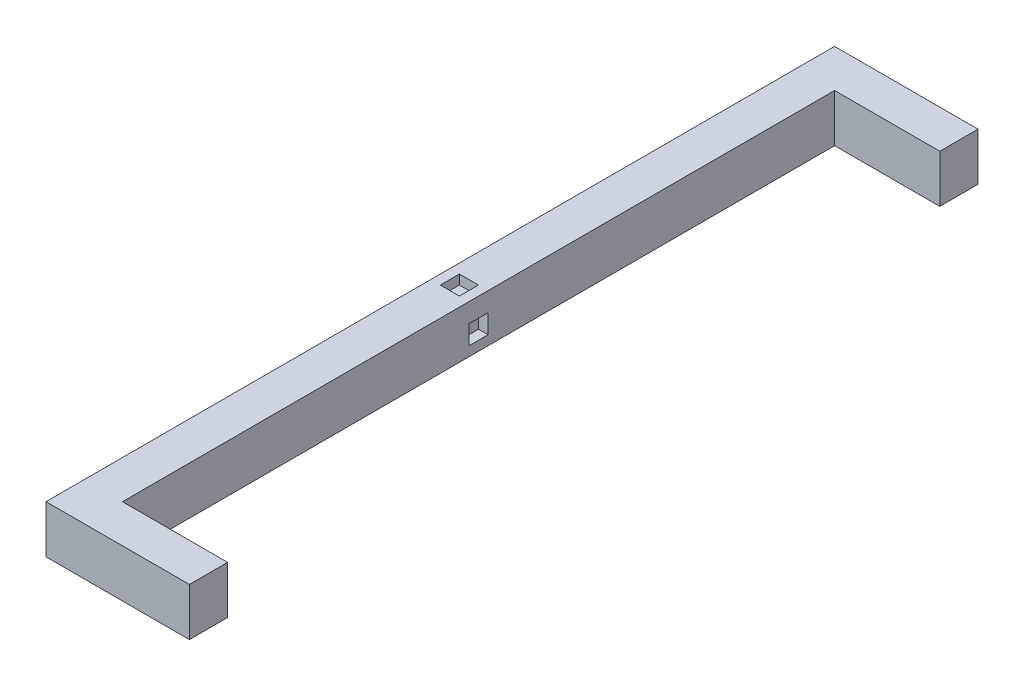
SolidWorks part; units mm, degrees
ref_plane "Front Plane" through (0, 0, 0) normal (0, 0, 1) x (1, 0, 0)
ref_plane "Top Plane" through (0, 0, 0) normal (0, 1, 0) x (1, 0, 0)
ref_plane "Right Plane" through (0, 0, 0) normal (1, 0, 0) x (0, 0, -1)
sketch "Sketch1" plane through (0, 0, 0) normal (0, 0, 1) x (1, 0, 0)
  line L1 (0, 0) -> (8, 0)
  line L2 (0, 0) -> (0, 10)
  line L3 (0, 10) -> (8, 10)
  line L4 (8, 0) -> (8, 10)
  dimension "D1" = 8
  dimension "D2" = 10
extrude "Boss-Extrude1" add sketch "Sketch1" along normal blind 165
sketch "Sketch2" plane through (8, 0, 0) normal (1, 0, 0) x (0, 0, -1)
  line L0 (-82.5, 10) -> (-82.5, 0) construction
  line L1 (-165, 10) -> (0, 10) construction
  line L2 (-165, 0) -> (0, 0) construction
  line L3 (0, 10) -> (-8, 10)
  line L4 (-165, 0) -> (-157, 0)
  line L5 (-165, 0) -> (-165, 10)
  line L6 (-165, 10) -> (-157, 10)
  line L7 (-157, 0) -> (-157, 10)
  line L8 (-8, 0) -> (-8, 10)
  line L9 (0, 0) -> (-8, 0)
  line L10 (0, 0) -> (0, 10)
  dimension "D1" = 8
extrude "Boss-Extrude2" add sketch "Sketch2" along normal blind 22
sketch "Sketch3" plane through (0, 10, 0) normal (0, 1, 0) x (1, 0, 0)
  line L0 (8, -82.5) -> (0, -82.5) construction
  line L1 (8, -157) -> (8, -8) construction
  line L2 (0, -165) -> (0, 0) construction
  line L4 (6, -84.5) -> (2, -84.5)
  line L5 (6, -84.5) -> (6, -80.5)
  line L6 (6, -80.5) -> (2, -80.5)
  line L7 (2, -84.5) -> (2, -80.5)
  line L8 (6, -84.5) -> (2, -80.5) construction
  line L9 (6, -80.5) -> (2, -84.5) construction
  point P6 (4, -82.5)
  dimension "D1" = 4
  dimension "D2" = 4
extrude "Cut-Extrude1" cut sketch "Sketch3" against normal blind 2
sketch "Sketch5" plane through (8, 0, 0) normal (1, 0, 0) x (0, 0, -1)
  line L0 (-82.5, 0) -> (-82.5, 4) construction
  line L1 (-157, 0) -> (-8, 0) construction
  line L3 (-80.5, 2) -> (-84.5, 2)
  line L4 (-80.5, 2) -> (-80.5, 6)
  line L5 (-80.5, 6) -> (-84.5, 6)
  line L6 (-84.5, 2) -> (-84.5, 6)
  line L7 (-80.5, 2) -> (-84.5, 6) construction
  line L8 (-80.5, 6) -> (-84.5, 2) construction
  dimension "D1" = 4
  dimension "D2" = 4
  dimension "D3" = 4
extrude "Cut-Extrude2" cut sketch "Sketch5" against normal blind 2
